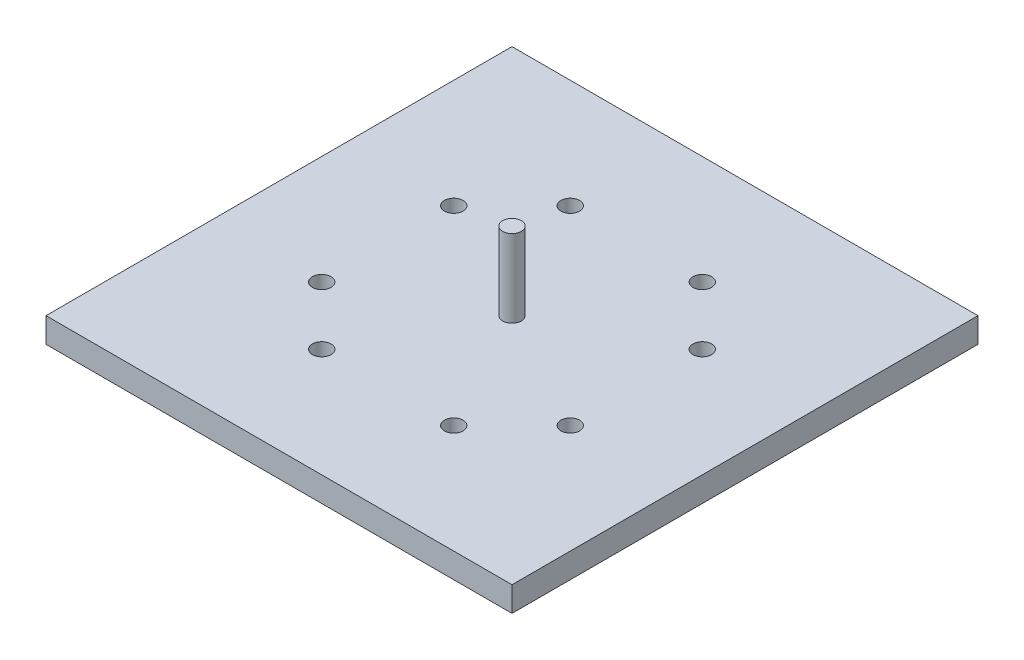
SolidWorks part; units mm, degrees
ref_plane "Front Plane" through (0, 0, 0) normal (0, 0, 1) x (1, 0, 0)
ref_plane "Top Plane" through (0, 0, 0) normal (0, 1, 0) x (1, 0, 0)
ref_plane "Right Plane" through (0, 0, 0) normal (1, 0, 0) x (0, 0, -1)
sketch "Sketch1" plane through (0, 0, 0) normal (0, 1, 0) x (1, 0, 0)
  line L0 (15, 0) -> (15, 30) construction
  line L1 (0, 0) -> (30, 0)
  line L2 (0, 0) -> (0, 30)
  line L3 (0, 30) -> (30, 30)
  line L4 (30, 0) -> (30, 30)
  line L5 (15, 13) -> (19.25, 13)
  dimension "D1" = 30
  dimension "D2" = 30
  dimension "D3" = 4.25
  dimension "D4" = 13
extrude "Boss-Extrude1" add sketch "Sketch1" along normal blind 1.6
sketch "Sketch2" plane through (0, 1.6, 0) normal (0, 1, 0) x (1, 0, 0)
  line L0 (15, 30) -> (15, 0) construction
  line L1 (0, 30) -> (30, 30) construction
  line L2 (0, 0) -> (30, 0) construction
  line L3 (15, 7) -> (19.25, 7) construction
  line L4 (30, 15) -> (0, 15) construction
  line L5 (30, 0) -> (30, 30) construction
  line L6 (0, 0) -> (0, 30) construction
  circle A0 centre (19.25, 7) radius 0.6
  circle A1 centre (10.75, 7) radius 0.6
  circle A2 centre (19.25, 23) radius 0.6
  circle A3 centre (10.75, 23) radius 0.6
  dimension "D3" = 1.2
  dimension "D1" = 4.25
  dimension "D2" = 7
extrude "Cut-Extrude1" cut sketch "Sketch2" against normal blind 1.6
pattern_circular "CirPattern1" count 2 every 90 about axis through (15, 0, -15) along (0, 1, 0) of "Cut-Extrude1"
sketch "Sketch4" plane through (0, 1.6, 0) normal (0, 1, 0) x (1, 0, 0)
  line L0 (0, 15) -> (30, 15) construction
  line L1 (0, 0) -> (0, 30) construction
  line L2 (30, 0) -> (30, 30) construction
  line L3 (15, 0) -> (15, 15) construction
  line L4 (0, 0) -> (30, 0) construction
  circle A0 centre (15, 15) radius 0.6
  dimension "D1" = 1.2
extrude "Boss-Extrude2" add sketch "Sketch4" along normal blind 5
